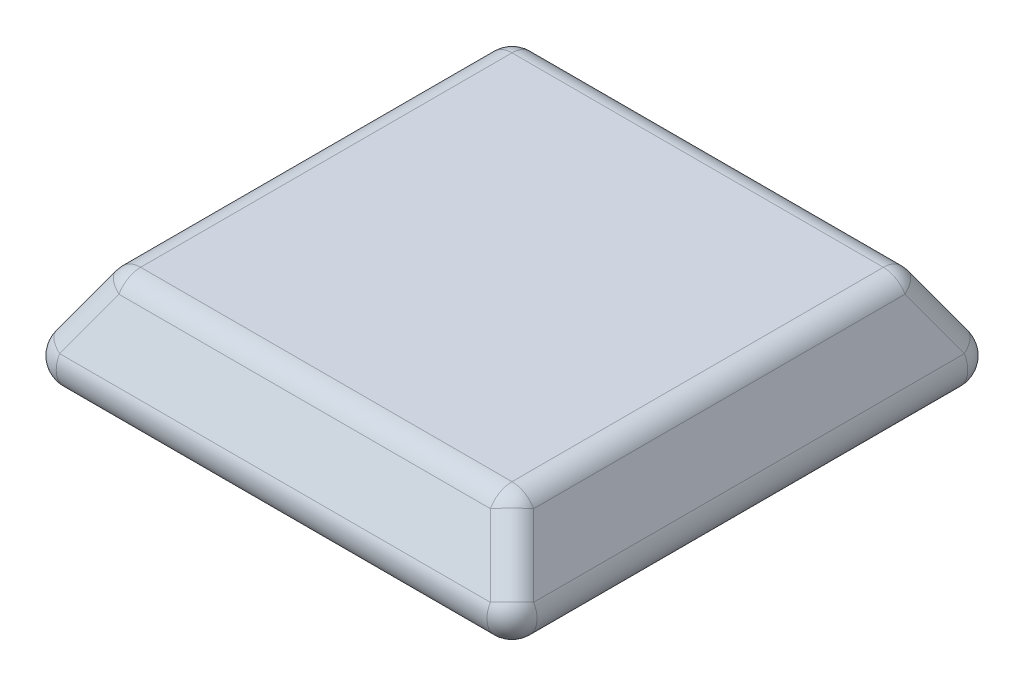
SolidWorks part; units mm, degrees
ref_plane "Front Plane" through (0, 0, 0) normal (0, 0, 1) x (1, 0, 0)
ref_plane "Top Plane" through (0, 0, 0) normal (0, 1, 0) x (1, 0, 0)
ref_plane "Right Plane" through (0, 0, 0) normal (1, 0, 0) x (0, 0, -1)
sketch "Sketch2" plane through (0, 0, 0) normal (0, 1, 0) x (1, 0, 0)
  line L1 (-3100, 3100) -> (3100, 3100)
  line L2 (-3100, 3100) -> (-3100, -3100)
  line L3 (-3100, -3100) -> (3100, -3100)
  line L4 (3100, 3100) -> (3100, -3100)
  line L5 (-3100, 3100) -> (3100, -3100) construction
  line L6 (-3100, -3100) -> (3100, 3100) construction
  point P0 (0, 0)
  dimension "D1" = 6200
  dimension "D2" = 6200
extrude "Boss-Extrude1" add sketch "Sketch2" along normal blind 1216 draft 30
fillet "Fillet1" radius 300 12 edges at (0, 0, -3100) (3100, 0, 0) (0, 0, 3100) (-3100, 0, 0) (-2748.971, 608, -2748.971) (2748.971, 608, -2748.971) (-2748.971, 608, 2748.971) (2748.971, 608, 2748.971) (2397.9421, 1216, 0) (0, 1216, -2397.9421) (-2397.9421, 1216, 0) (0, 1216, 2397.9421)
sketch "Sketch3" plane through (0, 1216, 0) normal (0, 1, 0) x (1, 0, 0)
  line L0 (0, 0) -> (-1770.3644, 0)
  circle A0 centre (0, 0) radius 400
sketch "Sketch4" plane through (0, 0, 0) normal (0, -1, 0) x (1, 0, 0)
  line L0 (0, 0) -> (0, 763.0725)
  circle A0 centre (0, 0) radius 200
